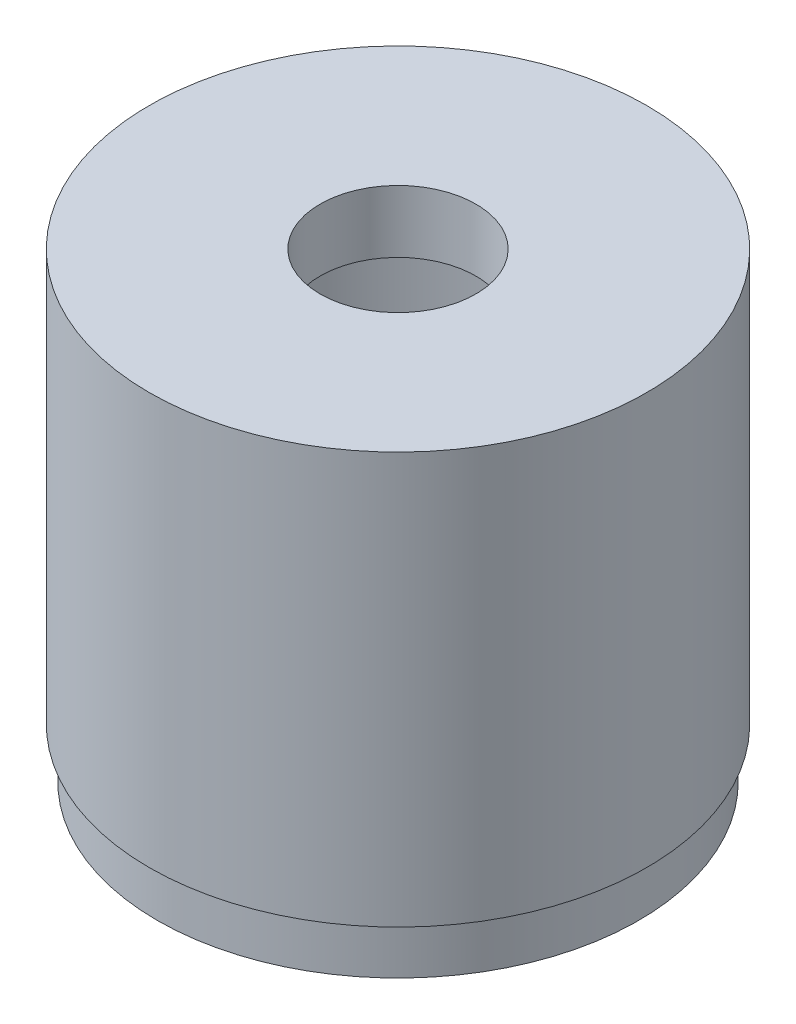
SolidWorks part; units mm, degrees
ref_plane "Front Plane" through (0, 0, 0) normal (0, 0, 1) x (1, 0, 0)
ref_plane "Top Plane" through (0, 0, 0) normal (0, 1, 0) x (1, 0, 0)
ref_plane "Right Plane" through (0, 0, 0) normal (1, 0, 0) x (0, 0, -1)
sketch "Sketch1" plane through (0, 0, 0) normal (0, 1, 0) x (1, 0, 0)
  circle A0 centre (0, 0) radius 24.511
  circle A1 centre (0, 0) radius 21.971
  dimension "D1" = 49.022
  dimension "D2" = 2.54
extrude "Boss-Extrude1" add sketch "Sketch1" along normal blind 40.64
sketch "Sketch2" plane through (0, 40.64, 0) normal (0, 1, 0) x (1, 0, 0)
  circle A0 centre (0, 0) radius 24.511 construction
  circle A1 centre (0, 0) radius 24.511
extrude "Boss-Extrude2" add sketch "Sketch2" along normal blind 6.35
sketch "Sketch3" plane through (0, 46.99, 0) normal (0, 1, 0) x (1, 0, 0)
  circle A0 centre (0, 0) radius 7.9375
  dimension "D1" = 15.875
extrude "Cut-Extrude1" cut sketch "Sketch3" against normal up to next
sketch "Sketch4" plane through (0, 46.99, 0) normal (0, 1, 0) x (1, 0, 0)
  circle A0 centre (0, 0) radius 24.511 construction
  circle A1 centre (0, 0) radius 24.511
  circle A2 centre (0, 0) radius 25.3365
  dimension "D1" = 50.673
extrude "Boss-Extrude3" add sketch "Sketch4" against normal blind 41.91
